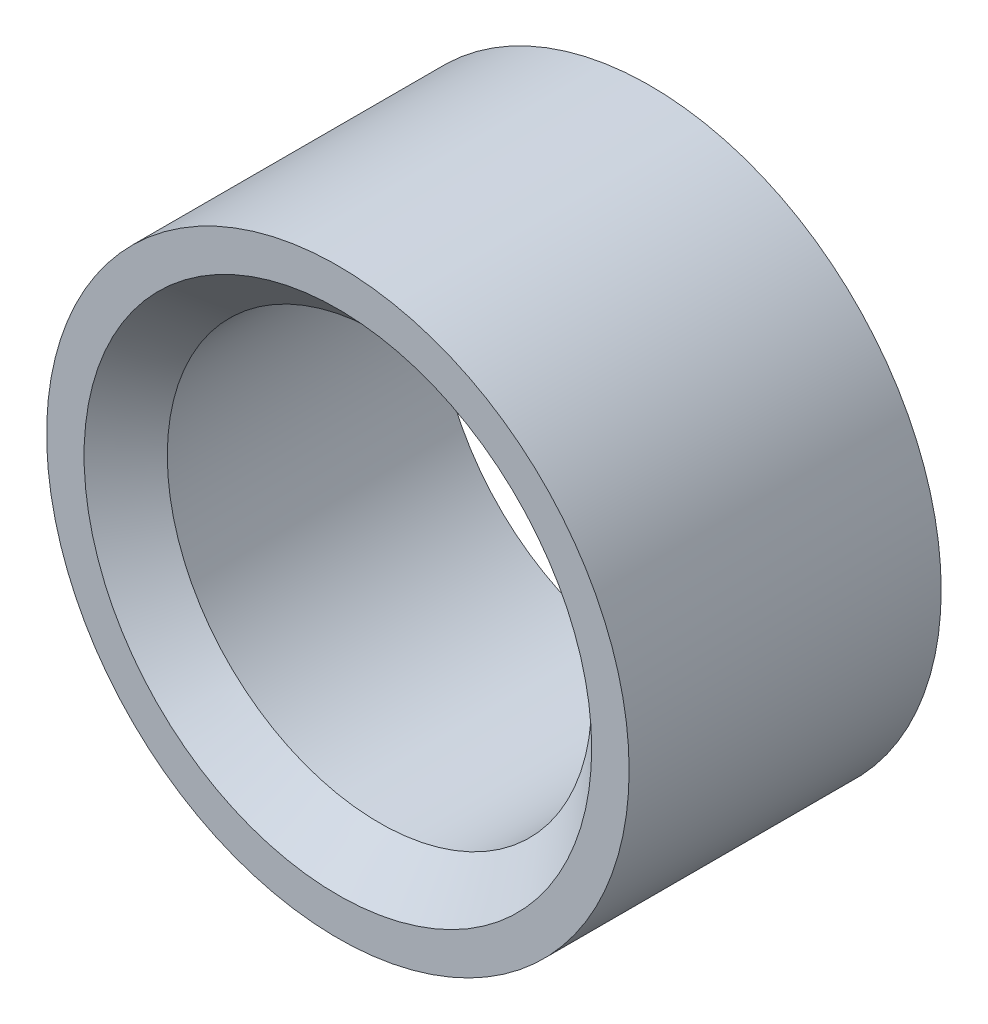
SolidWorks part; units mm, degrees
material "6061 Alloy"
ref_plane "前视基准面" through (0, 0, 0) normal (0, 0, 1) x (1, 0, 0)
ref_plane "上视基准面" through (0, 0, 0) normal (0, 1, 0) x (1, 0, 0)
ref_plane "右视基准面" through (0, 0, 0) normal (1, 0, 0) x (0, 0, -1)
sketch "草图1" plane through (0, 0, 0) normal (0, 0, 1) x (1, 0, 0)
  circle A0 centre (0, 0) radius 14
  circle A1 centre (0, 0) radius 10.2
extrude "凸台-拉伸1" add sketch "草图1" along normal blind 15
chamfer "倒角1" distance 2 angle 45 1 edges at (10.2, 0, 15)
